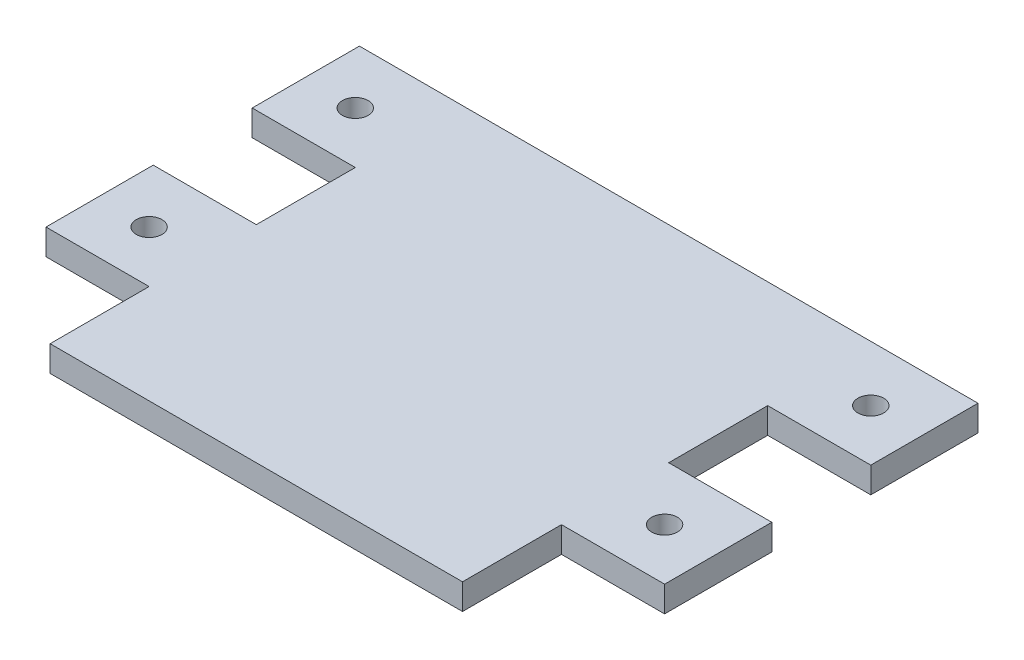
SolidWorks part; units mm, degrees
ref_plane "Front Plane" through (0, 0, 0) normal (0, 0, 1) x (1, 0, 0)
ref_plane "Top Plane" through (0, 0, 0) normal (0, 1, 0) x (1, 0, 0)
ref_plane "Right Plane" through (0, 0, 0) normal (1, 0, 0) x (0, 0, -1)
sketch "Sketch1" plane through (0, 0, 0) normal (0, 1, 0) x (1, 0, 0)
  line L1 (0, 0) -> (50.8, 0)
  line L2 (0, 0) -> (0, 50.8)
  line L3 (0, 50.8) -> (50.8, 50.8)
  line L4 (50.8, 0) -> (50.8, 50.8)
  dimension "D1" = 50.8
  dimension "D2" = 50.8
extrude "Boss-Extrude1" add sketch "Sketch1" along normal blind 3.175
sketch "Sketch2" plane through (0, 3.175, 0) normal (0, 1, 0) x (1, 0, 0)
  line L1 (50.8, 50.8) -> (63.5, 50.8)
  line L2 (50.8, 50.8) -> (50.8, 37.592)
  line L3 (50.8, 37.592) -> (63.5, 37.592)
  line L4 (63.5, 50.8) -> (63.5, 37.592)
  circle A0 centre (57.15, 43.942) radius 1.5875
  dimension "D3" = 3.175
  dimension "D4" = 6.35
  dimension "D5" = 6.35
  dimension "D1" = 13.208
  dimension "D2" = 12.7
extrude "Boss-Extrude2" add sketch "Sketch2" against normal blind 3.175
pattern_linear "LPattern1" count 2 spacing 25.4 along (0, 0, 1) of "Boss-Extrude2"
ref_plane "Plane1" through (25.4, 0, 0) normal (-1, 0, 0) x (0, 0, 1)
mirror "Mirror1" about plane through (25.4, 0, 0) normal (-1, 0, 0) of "LPattern1", "Boss-Extrude2"
